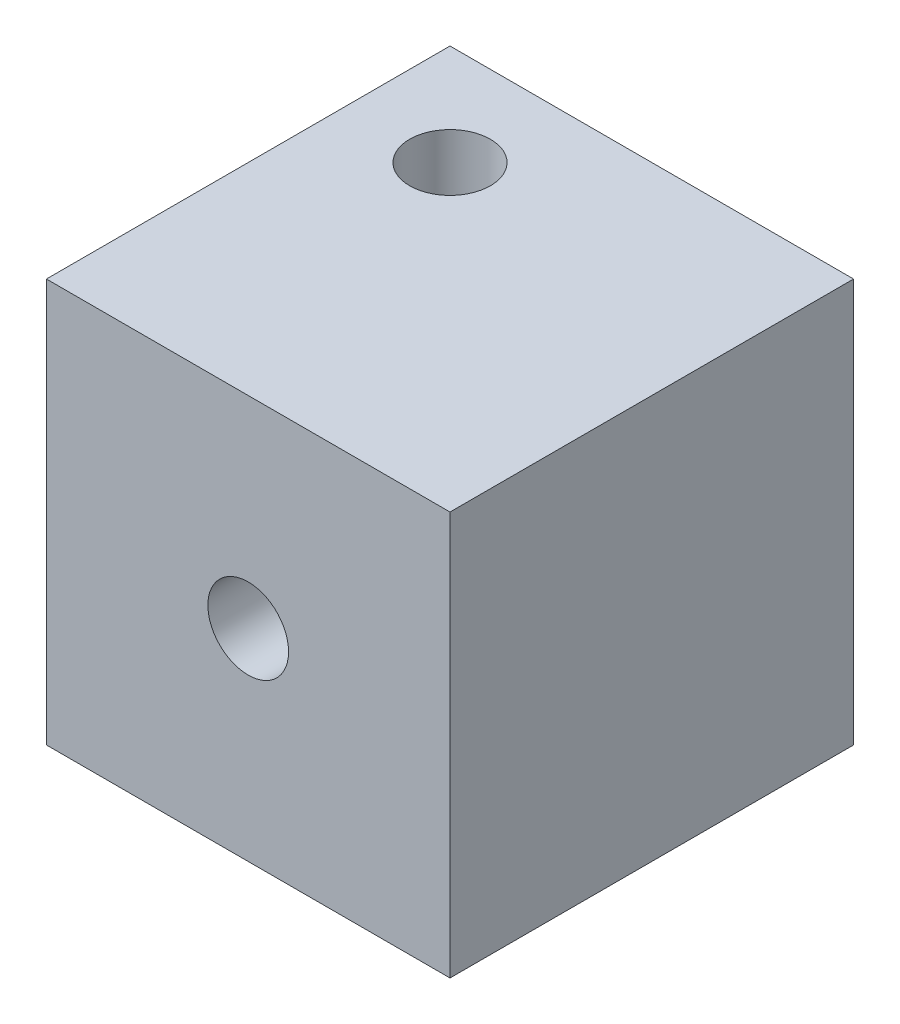
SolidWorks part; units mm, degrees
ref_plane "Plan de face" through (0, 0, 0) normal (0, 0, 1) x (1, 0, 0)
ref_plane "Plan de dessus" through (0, 0, 0) normal (0, 1, 0) x (1, 0, 0)
ref_plane "Plan de droite" through (0, 0, 0) normal (1, 0, 0) x (0, 0, -1)
sketch "Esquisse2" plane through (0, 0, 0) normal (0, 0, 1) x (1, 0, 0)
  line L1 (-100, 100) -> (0, 100)
  line L2 (-100, 100) -> (-100, 0)
  line L3 (-100, 0) -> (0, 0)
  line L4 (0, 100) -> (0, 0)
  dimension "D1" = 100
  dimension "D2" = 100
extrude "Boss.-Extru.1" add sketch "Esquisse2" along normal blind 100
sketch "Esquisse3" plane through (0, 0, 100) normal (0, 0, 1) x (1, 0, 0)
  line L0 (0, 100) -> (-100, 100) construction
  line L1 (-100, 100) -> (-100, 0) construction
  circle A0 centre (-50, 50) radius 10
  dimension "D1" = 20
  dimension "D2" = 50
  dimension "D3" = 50
extrude "Enlèv. mat.-Extru.1" cut sketch "Esquisse3" against normal through all
sketch "Esquisse4" plane through (0, 100, 0) normal (0, 1, 0) x (1, 0, 0)
  line L0 (0, 0) -> (-100, 0) construction
  line L1 (-100, -100) -> (-100, 0) construction
  circle A0 centre (-75, -25) radius 10
  point P6 (-36.7112, -36.0849)
  point P7 (-26.4404, -23.6848)
  dimension "D1" = 20
  dimension "D2" = 25
  dimension "D3" = 25
extrude "Enlèv. mat.-Extru.2" cut sketch "Esquisse4" against normal through all
